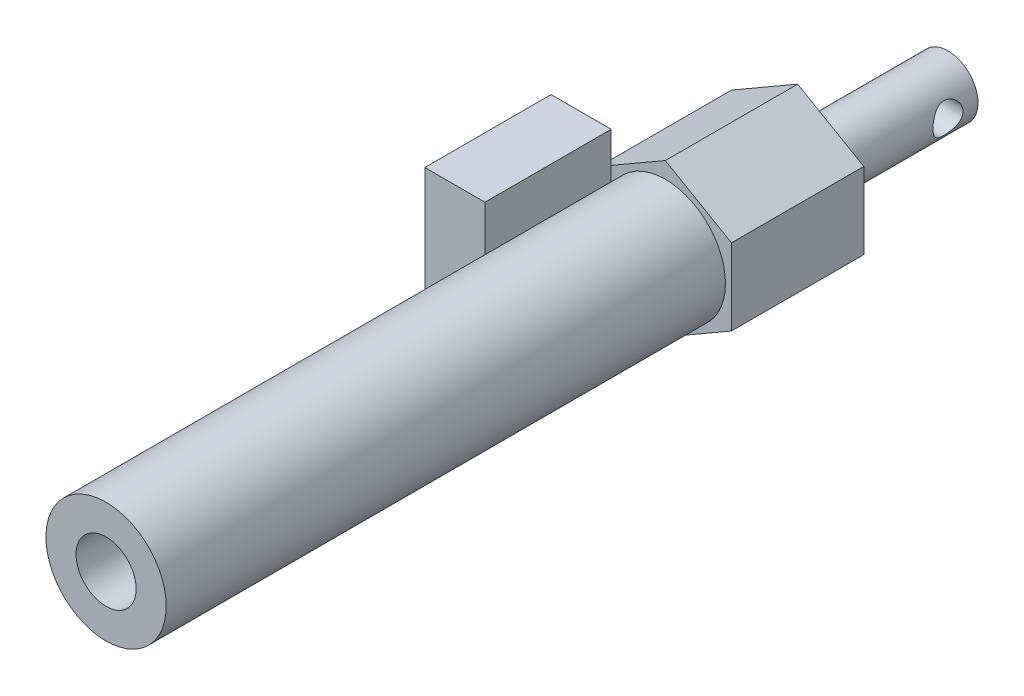
SolidWorks part; units mm, degrees
ref_plane "Front Plane" through (0, 0, 0) normal (0, 0, 1) x (1, 0, 0)
ref_plane "Top Plane" through (0, 0, 0) normal (0, 1, 0) x (1, 0, 0)
ref_plane "Right Plane" through (0, 0, 0) normal (1, 0, 0) x (0, 0, -1)
sketch "Sketch1" plane through (0, 0, 0) normal (0, 0, 1) x (1, 0, 0)
  circle A0 centre (0, 0) radius 10
  dimension "D1" = 20
extrude "Boss-Extrude1" add sketch "Sketch1" along normal blind 115
sketch "Sketch2" plane through (0, 0, 0) normal (0, 0, -1) x (-1, 0, 0)
  circle A0 centre (0, 0) radius 5
  dimension "D1" = 10
extrude "Boss-Extrude2" add sketch "Sketch2" along normal blind 25
sketch "Sketch3" plane through (0, 0, 115) normal (0, 0, 1) x (1, 0, 0)
  circle A0 centre (0, 0) radius 5
  dimension "D1" = 10
extrude "Cut-Extrude1" cut sketch "Sketch3" against normal blind 110
sketch "Sketch4" plane through (0, 0, 0) normal (1, 0, 0) x (0, 0, -1)
  line L0 (25, 5) -> (0, 5) construction
  line L1 (25, -5) -> (25, 5) construction
  circle A0 centre (20, 0) radius 2.5
  dimension "D1" = 5
  dimension "D2" = 5
  dimension "D3" = 5
extrude "Cut-Extrude2" cut sketch "Sketch4" against normal through all both and the other way through all
sketch "Sketch5" plane through (0, 0, 0) normal (0, 0, -1) x (-1, 0, 0)
  line L1 (0, -12.7017) -> (11, -6.3509)
  line L2 (11, -6.3509) -> (11, 6.3509)
  line L3 (11, 6.3509) -> (0, 12.7017)
  line L4 (0, 12.7017) -> (-11, 6.3509)
  line L5 (-11, 6.3509) -> (-11, -6.3509)
  line L6 (-11, -6.3509) -> (0, -12.7017)
  circle A0 centre (0, 0) radius 11 construction
  circle A1 centre (0, 0) radius 10
  dimension "D1" = 22
  dimension "D2" = 20
extrude "Boss-Extrude3" add sketch "Sketch5" against normal blind 22
sketch "Sketch6" plane through (-11, 0, 0) normal (-1, 0, 0) x (0, 0, 1)
  line L0 (22, -10) -> (22, 10) construction
  line L1 (22, -8.2983) -> (43, -8.2983)
  line L2 (22, -8.2983) -> (22, 12.7017)
  line L3 (22, 12.7017) -> (43, 12.7017)
  line L4 (43, -8.2983) -> (43, 12.7017)
  line L5 (22, 12.7017) -> (0, 12.7017) construction
  dimension "D1" = 21
  dimension "D2" = 21
extrude "Boss-Extrude4" add sketch "Sketch6" along normal blind 8 separate body
sketch "Sketch7" plane through (-11, 0, 0) normal (1, 0, 0) x (0, 0, -1)
  line L4 (-22, -8.2983) -> (-22, 12.7017)
  line L5 (-22, 12.7017) -> (-43, 12.7017)
  line L6 (-43, 12.7017) -> (-43, -8.2983)
  line L7 (-43, -8.2983) -> (-22, -8.2983)
  line L8 (-22, -8.2983) -> (-22, 12.7017)
  line L9 (-22, 12.7017) -> (-43, 12.7017)
  line L10 (-43, 12.7017) -> (-43, -8.2983)
  line L11 (-43, -8.2983) -> (-22, -8.2983)
  dimension "D1" = 0
extrude "Boss-Extrude5" add sketch "Sketch7" along normal blind 2
sketch "Sketch8" plane through (-19, 0, 0) normal (-1, 0, 0) x (0, 0, 1)
  line L0 (43, -8.2983) -> (43, 12.7017) construction
  line L1 (43, 12.7017) -> (22, 12.7017) construction
  circle A0 centre (36.5, 6.2017) radius 5
  circle A1 centre (36.5, 6.2017) radius 4
  dimension "D1" = 10
  dimension "D2" = 8
  dimension "D3" = 6.5
  dimension "D4" = 6.5
extrude "Cut-Extrude3" cut sketch "Sketch8" against normal blind 2
sketch "Sketch9" plane through (-19, 0, 0) normal (-1, 0, 0) x (0, 0, 1)
  circle A0 centre (36.5, 6.2017) radius 1.5451
extrude "Cut-Extrude4" cut sketch "Sketch9" against normal blind 2
